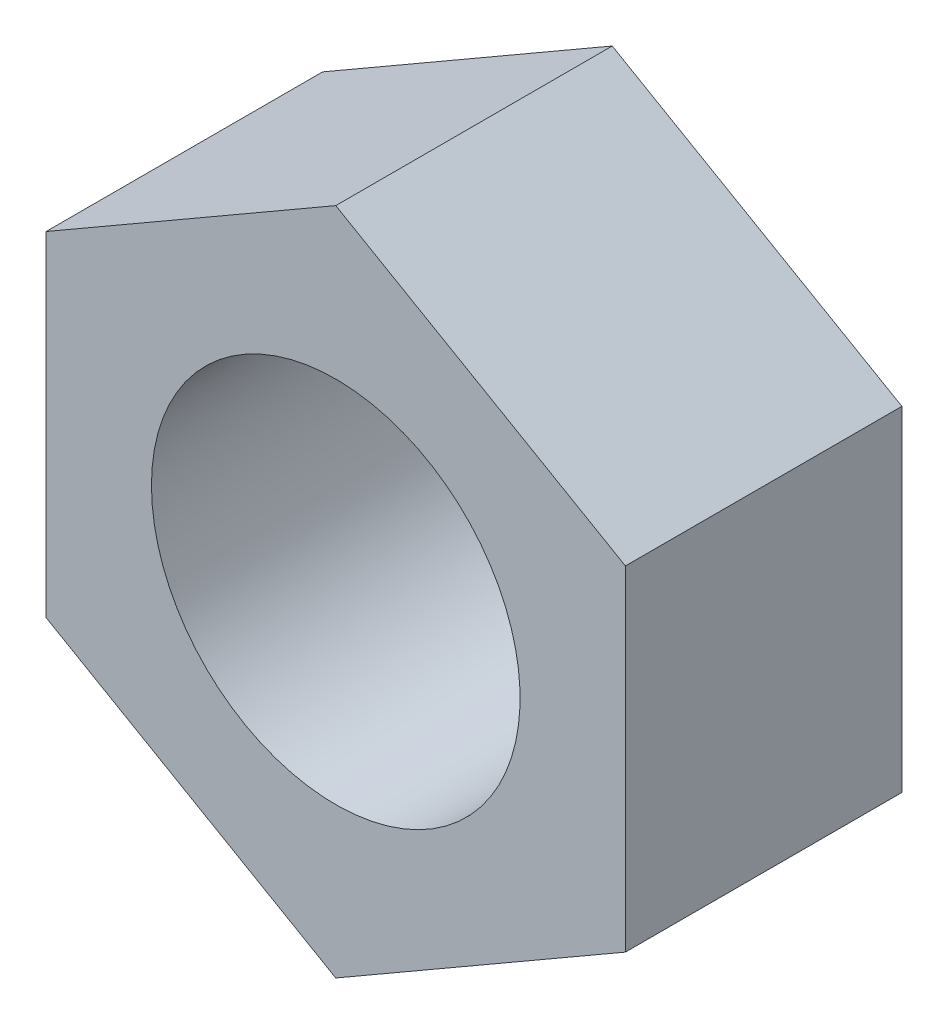
SolidWorks part; units mm, degrees
ref_plane "前视基准面" through (0, 0, 0) normal (0, 0, 1) x (1, 0, 0)
ref_plane "上视基准面" through (0, 0, 0) normal (0, 1, 0) x (1, 0, 0)
ref_plane "右视基准面" through (0, 0, 0) normal (1, 0, 0) x (0, 0, -1)
sketch "草图1" plane through (0, 0, 0) normal (0, 0, 1) x (1, 0, 0)
  line L0 (37.3155, 15.1595) -> (37.3155, 2.4578)
  line L1 (15.3155, 15.1595) -> (15.3155, 2.4578)
  line L2 (37.3155, 15.1595) -> (26.3155, 21.5104)
  line L3 (26.3155, 21.5104) -> (15.3155, 15.1595)
  line L4 (15.3155, 2.4578) -> (26.3155, -3.893)
  line L5 (26.3155, -3.893) -> (37.3155, 2.4578)
  line L6 (26.3155, 8.8087) -> (31.8155, -0.7176)
  line L7 (26.3155, 8.8087) -> (31.8155, 18.335)
  circle A0 centre (26.3155, 8.8087) radius 7
  dimension "D1" = 14
  dimension "D2" = 11
extrude "凸台-拉伸1" add sketch "草图1" along normal blind 10.5 contours L0 L5 L4 L1 L3 L2
sketch "草图2" plane through (0, 0, 0) normal (0, 0, -1) x (-1, 0, 0)
  line L0 (-31.8155, -0.7176) -> (-20.8155, 18.335) construction
  line L1 (-26.3155, -3.893) -> (-37.3155, 2.4578) construction
  line L2 (-26.3155, 21.5104) -> (-15.3155, 15.1595) construction
  circle A0 centre (-26.3155, 8.8087) radius 7
extrude "切除-拉伸1" cut sketch "草图2" against normal blind 10.5
